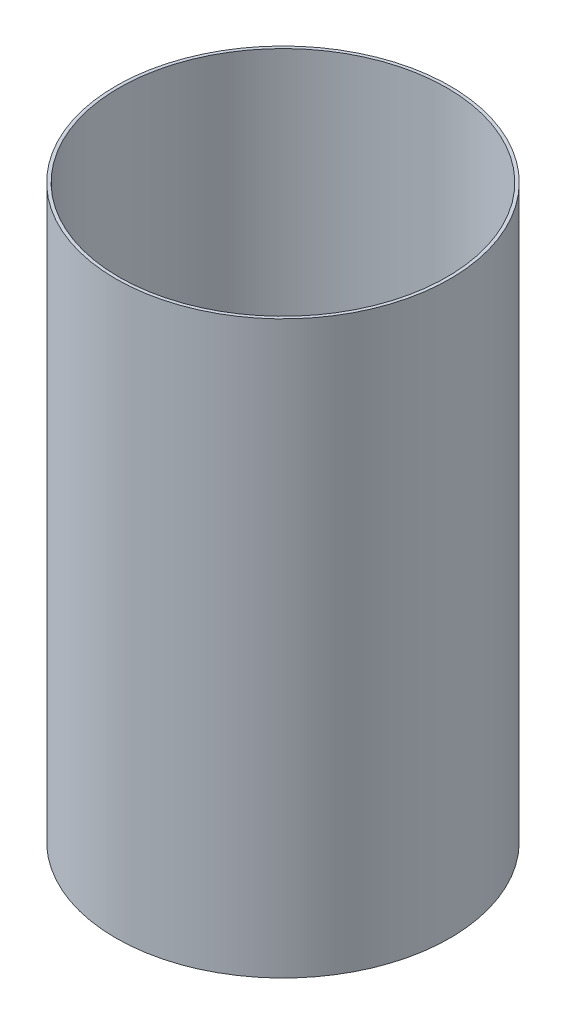
SolidWorks part; units mm, degrees
material "75mm-CastingTube"
ref_plane "Front Plane" through (0, 0, 0) normal (0, 0, 1) x (1, 0, 0)
ref_plane "Top Plane" through (0, 0, 0) normal (0, 1, 0) x (1, 0, 0)
ref_plane "Right Plane" through (0, 0, 0) normal (1, 0, 0) x (0, 0, -1)
sketch "Sketch1" plane through (0, 0, 0) normal (0, 1, 0) x (1, 0, 0)
  circle A0 centre (0, 0) radius 32.4612
  circle A1 centre (0, 0) radius 33.0835
  dimension "D1" = 64.9224
  dimension "D2" = 66.167
extrude "Boss-Extrude1" add sketch "Sketch1" along normal blind 113.03
